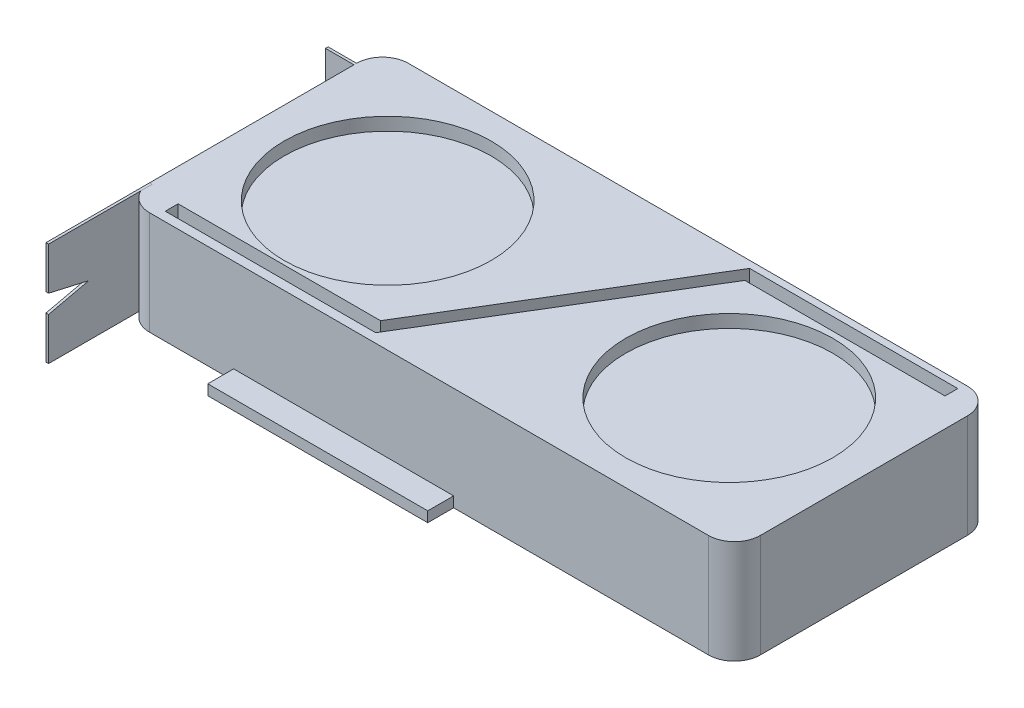
SolidWorks part; units mm, degrees
ref_plane "Front Plane" through (0, 0, 0) normal (0, 0, 1) x (1, 0, 0)
ref_plane "Top Plane" through (0, 0, 0) normal (0, 1, 0) x (1, 0, 0)
ref_plane "Right Plane" through (0, 0, 0) normal (1, 0, 0) x (0, 0, -1)
sketch "Sketch1" plane through (0, 0, 0) normal (0, 1, 0) x (1, 0, 0)
  line L1 (-118, 50) -> (118, 50)
  line L2 (-118, 50) -> (-118, -50)
  line L3 (-118, -50) -> (118, -50)
  line L4 (118, 50) -> (118, -50)
  line L5 (-118, 50) -> (118, -50) construction
  line L6 (-118, -50) -> (118, 50) construction
  point P0 (0, 0)
  dimension "D1" = 236
  dimension "D2" = 100
extrude "Boss-Extrude1" add sketch "Sketch1" along normal blind 40
sketch "Sketch2" plane through (0, 40, 0) normal (0, 1, 0) x (1, 0, 0)
  line L4 (0, -2) -> (0, 2)
  line L8 (-66, 0) -> (0, 0) construction
  line L9 (0, 0) -> (66, 0) construction
  circle A0 centre (-66, 0) radius 40
  circle A1 centre (66, 0) radius 40
  dimension "D2" = 80
  dimension "D1" = 66
  dimension "D3" = 4
extrude "Cut-Extrude1" cut sketch "Sketch2" against normal blind 5 contours A0 | A1
fillet "Fillet1" radius 10 4 edges at (118, 20, 50) (118, 20, -50) (-118, 20, 50) (-118, 20, -50)
sketch "Sketch3" plane through (0, 40, 0) normal (0, 1, 0) x (1, 0, 0)
  line L0 (-105.4631, -41.5021) -> (-105.4631, -46.455)
  line L1 (-105.4631, -46.455) -> (-24.1389, -46.455)
  line L2 (-24.1389, -46.455) -> (29.6601, 42.356)
  line L3 (29.6601, 42.356) -> (107.0002, 42.356)
  line L4 (107.0002, 42.356) -> (107.0002, 47.309)
  line L5 (107.0002, 47.309) -> (26.5579, 47.309)
  line L6 (26.5579, 47.309) -> (-27.2411, -41.5021)
  line L7 (-27.2411, -41.5021) -> (-105.4631, -41.5021)
extrude "Cut-Extrude2" cut sketch "Sketch3" against normal blind 10
sketch "Sketch4" plane through (0, 0, 50) normal (0, 0, 1) x (1, 0, 0)
  line L0 (-118, 0) -> (-118, 40) construction
  line L1 (-75.5, 0) -> (9.5, 0)
  line L2 (-75.5, 0) -> (-75.5, 4)
  line L3 (-75.5, 4) -> (9.5, 4)
  line L4 (9.5, 0) -> (9.5, 4)
  line L5 (-108, 0) -> (108, 0) construction
  point P5 (0, 0)
  dimension "D1" = 42.5
  dimension "D2" = 4
  dimension "D3" = 85
extrude "Boss-Extrude2" add sketch "Sketch4" along normal blind 10
sketch "Sketch5" plane through (-118, 0, 0) normal (-1, 0, 0) x (0, 0, 1)
  line L0 (40, 40) -> (80, 40)
  line L1 (80, 40) -> (80, 23.5438)
  line L2 (80, 23.5438) -> (64.4647, 20)
  line L3 (64.4647, 20) -> (69.3151, 20) construction
  line L4 (64.4647, 20) -> (64.4647, 40) construction
  line L5 (64.4647, 20) -> (64.4647, 0) construction
  line L6 (40, 0) -> (80, 0)
  line L7 (80, 0) -> (80, 16.4562)
  line L8 (80, 16.4562) -> (64.4647, 20)
  line L9 (40, 40) -> (40, 0)
  line L10 (50, 40) -> (50, 0) construction
  line L11 (40, 0) -> (50, 0) construction
  dimension "D1" = 30
extrude "Boss-Extrude3" add sketch "Sketch5" against normal blind 1 separate body
sketch "Sketch6" plane through (-118, 0, 0) normal (-1, 0, 0) x (0, 0, 1)
  line L0 (-40, 0) -> (40, 0) construction
  line L1 (-40, 40) -> (-39, 40)
  line L2 (-40, 40) -> (-40, 0)
  line L3 (-40, 0) -> (-39, 0)
  line L4 (-39, 40) -> (-39, 0)
  dimension "D1" = 1
extrude "Boss-Extrude4" add sketch "Sketch6" along normal blind 11
